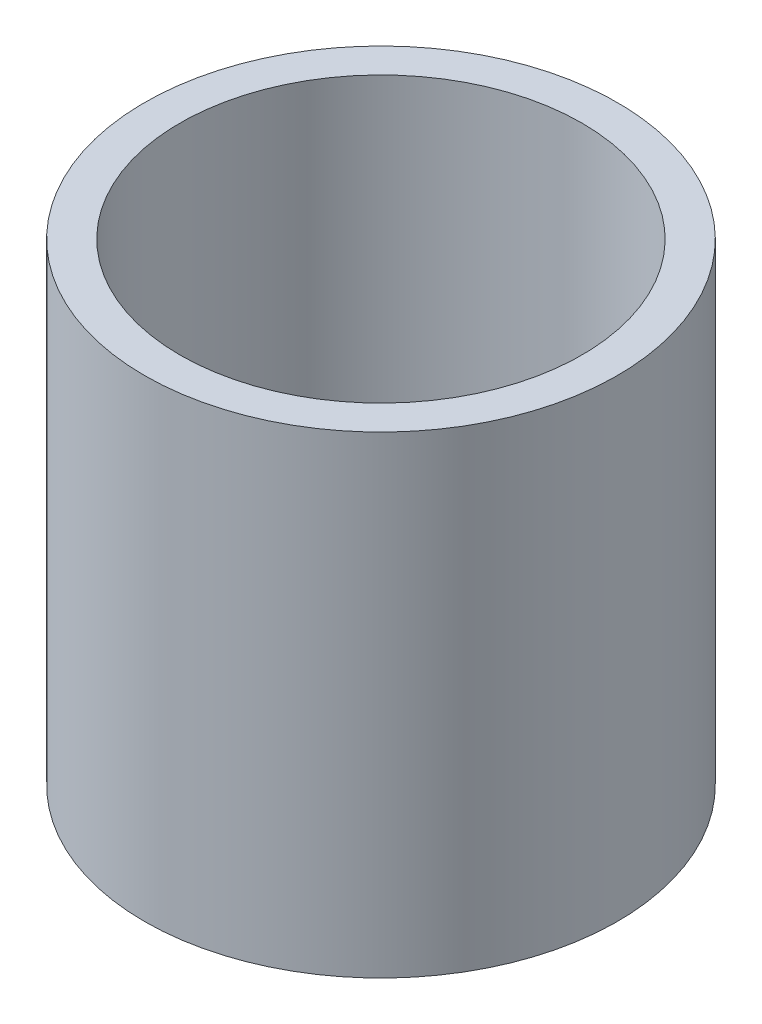
SolidWorks part; units mm, degrees
ref_plane "Plan de face" through (0, 0, 0) normal (0, 0, 1) x (1, 0, 0)
ref_plane "Plan de dessus" through (0, 0, 0) normal (0, 1, 0) x (1, 0, 0)
ref_plane "Plan de droite" through (0, 0, 0) normal (1, 0, 0) x (0, 0, -1)
sketch "Esquisse1" plane through (0, 0, 0) normal (0, 0, 1) x (1, 0, 0)
  line L0 (0, 0) -> (40, 0)
  line L1 (40, 0) -> (40, 80)
  line L2 (0, 5) -> (34, 5)
  line L3 (34, 5) -> (34, 80)
  line L4 (0, 5) -> (0, 0)
  line L5 (34, 80) -> (40, 80)
  dimension "D1" = 40
  dimension "D2" = 80
  dimension "D4" = 6
  dimension "D3" = 5
revolve "Révolution1" add sketch "Esquisse1" angle 360 about L4
